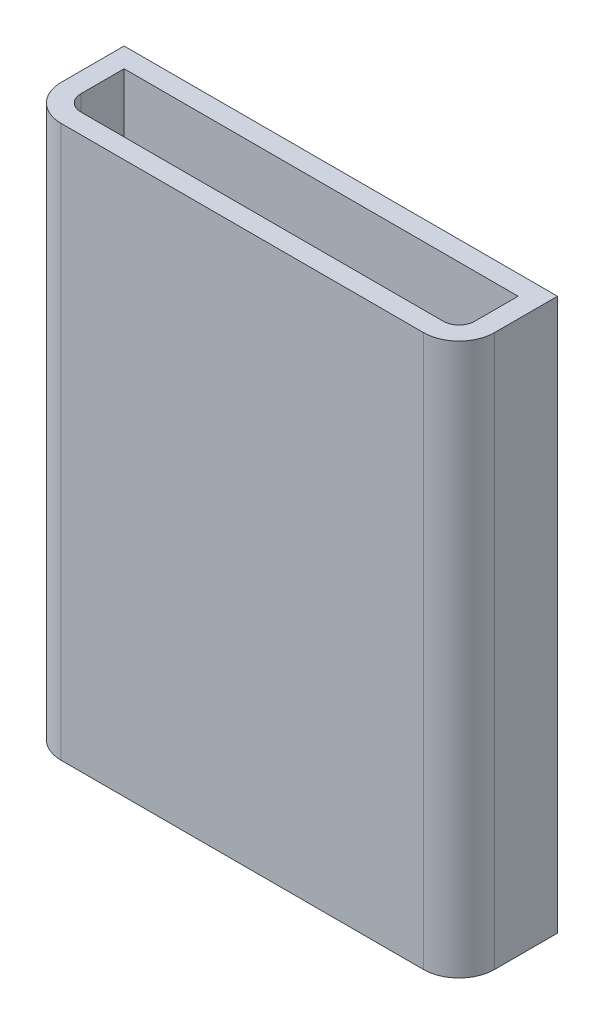
SolidWorks part; units mm, degrees
ref_plane "Front Plane" through (0, 0, 0) normal (0, 0, 1) x (1, 0, 0)
ref_plane "Top Plane" through (0, 0, 0) normal (0, 1, 0) x (1, 0, 0)
ref_plane "Right Plane" through (0, 0, 0) normal (1, 0, 0) x (0, 0, -1)
sketch "Sketch1" plane through (0, 0, 0) normal (0, 1, 0) x (1, 0, 0)
  line L0 (0, 6.985) -> (0, 2.54)
  line L1 (2.54, 0) -> (60.96, 0)
  line L3 (2.54, 9.525) -> (60.96, 9.525)
  line L4 (63.5, 2.54) -> (63.5, 6.985)
  line L5 (-3.175, 6.985) -> (-3.175, 2.54)
  line L6 (2.54, -3.175) -> (60.96, -3.175)
  line L7 (66.675, 2.54) -> (66.675, 6.985)
  line L8 (2.54, 12.7) -> (60.96, 12.7)
  line L9 (2.54, 12.7) -> (-3.175, 12.7)
  line L10 (-3.175, 12.7) -> (-3.175, 6.985)
  line L11 (60.96, 12.7) -> (66.675, 12.7)
  line L12 (66.675, 12.7) -> (66.675, 6.985)
  arc A0 (60.96, 9.525) -> (63.5, 6.985) centre (60.96, 6.985) cw
  arc A1 (60.96, 0) -> (63.5, 2.54) centre (60.96, 2.54) ccw
  arc A2 (0, 2.54) -> (2.54, 0) centre (2.54, 2.54) ccw
  arc A3 (0, 6.985) -> (2.54, 9.525) centre (2.54, 6.985) cw
  arc A4 (-3.175, 2.54) -> (2.54, -3.175) centre (2.54, 2.54) ccw
  arc A5 (60.96, -3.175) -> (66.675, 2.54) centre (60.96, 2.54) ccw
  arc A8 (-3.175, 6.985) -> (2.54, 12.7) centre (2.54, 6.985) cw construction
  arc A9 (60.96, 12.7) -> (66.675, 6.985) centre (60.96, 6.985) cw construction
  point P7 (63.5, 9.525)
  point P10 (63.5, 0)
  point P13 (0, 0)
  dimension "D3" = 2.54
  dimension "D4" = 3.175
  dimension "D1" = 63.5
  dimension "D2" = 9.525
extrude "Boss-Extrude1" add sketch "Sketch1" along normal blind 88.9 contours L8 L11 L12 L7 A5 L6 A4 L5 L10 L9
sketch "Sketch2" plane through (0, 88.9, 0) normal (0, 1, 0) x (1, 0, 0)
  line L0 (2.54, 9.525) -> (0, 9.525)
  line L1 (0, 9.525) -> (0, 6.985)
  line L2 (60.96, 9.525) -> (63.5, 9.525)
  line L3 (63.5, 9.525) -> (63.5, 6.985)
  line L4 (0, 6.985) -> (0, 2.54)
  line L5 (2.54, 0) -> (60.96, 0)
  line L6 (63.5, 2.54) -> (63.5, 6.985)
  line L7 (60.96, 9.525) -> (2.54, 9.525)
  line L8 (0, 6.985) -> (0, 2.54)
  line L9 (2.54, 0) -> (60.96, 0)
  line L10 (63.5, 2.54) -> (63.5, 6.985)
  line L11 (60.96, 9.525) -> (2.54, 9.525)
  arc A4 (0, 2.54) -> (2.54, 0) centre (2.54, 2.54) ccw
  arc A5 (60.96, 0) -> (63.5, 2.54) centre (60.96, 2.54) ccw
  arc A6 (63.5, 6.985) -> (60.96, 9.525) centre (60.96, 6.985) ccw
  arc A7 (2.54, 9.525) -> (0, 6.985) centre (2.54, 6.985) ccw
  arc A8 (0, 2.54) -> (2.54, 0) centre (2.54, 2.54) ccw
  arc A9 (60.96, 0) -> (63.5, 2.54) centre (60.96, 2.54) ccw
  dimension "D1" = 0
extrude "Cut-Extrude1" cut sketch "Sketch2" against normal blind 88.9
